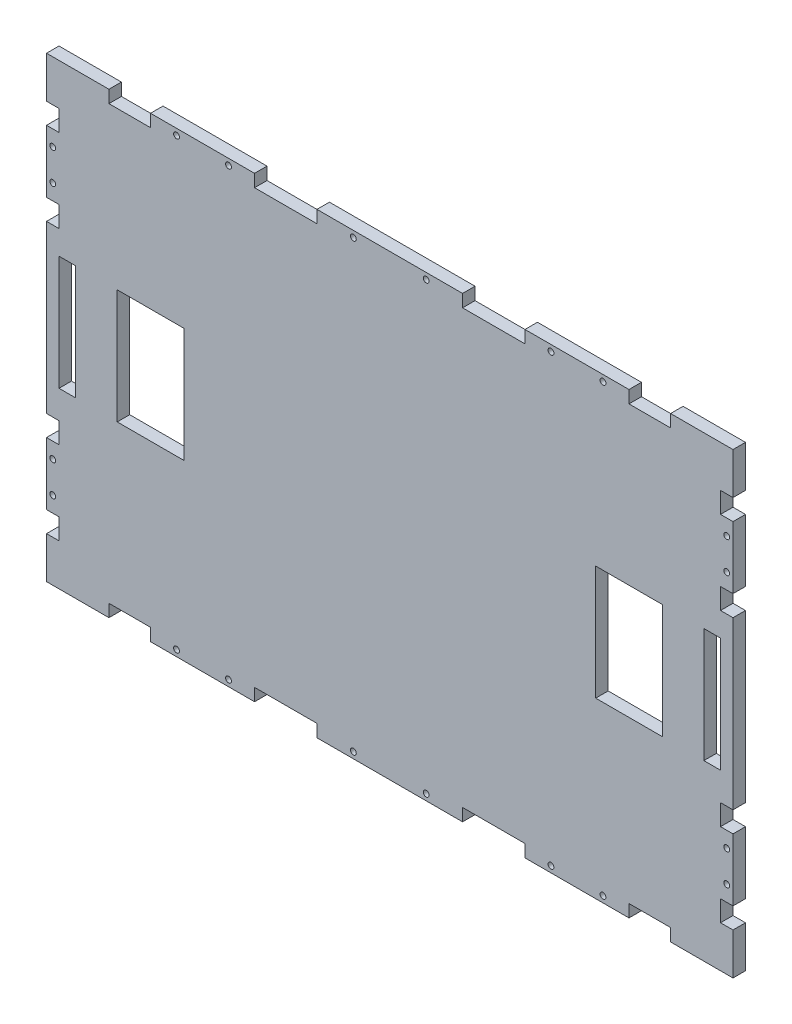
SolidWorks part; units mm, degrees
ref_plane "Plan de face" through (0, 0, 0) normal (0, 0, 1) x (1, 0, 0)
ref_plane "Plan de dessus" through (0, 0, 0) normal (0, 1, 0) x (1, 0, 0)
ref_plane "Plan de droite" through (0, 0, 0) normal (1, 0, 0) x (0, 0, -1)
sketch "Esquisse1" plane through (0, 0, 0) normal (0, 0, 1) x (1, 0, 0)
  line L0 (0, 124.9429) -> (0, -204.46) construction
  line L1 (-165, 110) -> (165, 110)
  line L2 (-165, 110) -> (-165, -110)
  line L3 (-165, -110) -> (165, -110)
  line L4 (165, 110) -> (165, -110)
  line L5 (-211.9802, 0) -> (248.5953, 0) construction
  dimension "D1" = 220
  dimension "D2" = 330
  dimension "D3" = 165
  dimension "D4" = 110
extrude "Boss.-Extru.1" add sketch "Esquisse1" along normal blind 6
sketch "Esquisse2" plane through (0, 0, 6) normal (0, 0, 1) x (1, 0, 0)
  line L0 (-165, 110) -> (-165, -110) construction
  line L1 (-159, 28.5) -> (-151, 28.5)
  line L2 (-159, 28.5) -> (-159, -26.5)
  line L3 (-159, -26.5) -> (-151, -26.5)
  line L4 (-151, 28.5) -> (-151, -26.5)
  line L5 (-131, 28.5) -> (-99, 28.5)
  line L6 (-131, 28.5) -> (-131, -26.5)
  line L7 (-131, -26.5) -> (-99, -26.5)
  line L8 (-99, 28.5) -> (-99, -26.5)
  line L9 (0, 145.0258) -> (0, -189.2208) construction
  line L10 (99, 28.5) -> (99, -26.5)
  line L11 (131, -26.5) -> (99, -26.5)
  line L12 (131, 28.5) -> (131, -26.5)
  line L13 (131, 28.5) -> (99, 28.5)
  line L14 (151, 28.5) -> (151, -26.5)
  line L15 (159, -26.5) -> (151, -26.5)
  line L16 (159, 28.5) -> (159, -26.5)
  line L17 (159, 28.5) -> (151, 28.5)
  line L18 (-165, -110) -> (165, -110) construction
  dimension "D1" = 6
  dimension "D2" = 8
  dimension "D3" = 20
  dimension "D4" = 32
  dimension "D5" = 99
  dimension "D6" = 55
  dimension "D7" = 55
  dimension "D8" = 83.5
  dimension "D9" = 83.5
extrude "Enlèv. mat.-Extru.1" cut sketch "Esquisse2" against normal blind 6
sketch "Esquisse3" plane through (0, 0, 6) normal (0, 0, 1) x (1, 0, 0)
  line L0 (0, 140.8551) -> (0, -222.4606) construction
  line L1 (330.3485, 0) -> (-244.4866, 0) construction
  line L2 (165, 110) -> (-165, 110) construction
  line L3 (-135, 110) -> (-115, 110)
  line L4 (-135, 110) -> (-135, 104)
  line L5 (-135, 104) -> (-115, 104)
  line L6 (-115, 110) -> (-115, 104)
  line L7 (-165, 110) -> (-165, -110) construction
  line L8 (-65, 110) -> (-35, 110)
  line L9 (-65, 110) -> (-65, 104)
  line L10 (-65, 104) -> (-35, 104)
  line L11 (-35, 110) -> (-35, 104)
  line L12 (-165, 50) -> (-159, 50)
  line L13 (-165, 50) -> (-165, 40)
  line L14 (-165, 40) -> (-159, 40)
  line L15 (-159, 50) -> (-159, 40)
  line L16 (35, 110) -> (35, 104)
  line L17 (-165, 90) -> (-159, 90)
  line L18 (-165, 90) -> (-165, 80)
  line L19 (-165, 80) -> (-159, 80)
  line L20 (-159, 90) -> (-159, 80)
  line L21 (65, 104) -> (35, 104)
  line L22 (65, 110) -> (35, 110)
  line L23 (159, 90) -> (159, 80)
  line L24 (165, 80) -> (159, 80)
  line L25 (165, 90) -> (165, 80)
  line L26 (165, 90) -> (159, 90)
  line L27 (159, 50) -> (159, 40)
  line L28 (165, 40) -> (159, 40)
  line L29 (165, 50) -> (165, 40)
  line L30 (165, 50) -> (159, 50)
  line L31 (65, 110) -> (65, 104)
  line L32 (115, 110) -> (115, 104)
  line L33 (135, 104) -> (115, 104)
  line L34 (135, 110) -> (135, 104)
  line L35 (135, 110) -> (115, 110)
  line L36 (135, -110) -> (115, -110)
  line L37 (135, -110) -> (135, -104)
  line L38 (135, -104) -> (115, -104)
  line L39 (115, -110) -> (115, -104)
  line L40 (65, -110) -> (65, -104)
  line L41 (165, -50) -> (159, -50)
  line L42 (165, -50) -> (165, -40)
  line L43 (165, -40) -> (159, -40)
  line L44 (159, -50) -> (159, -40)
  line L45 (165, -90) -> (159, -90)
  line L46 (165, -90) -> (165, -80)
  line L47 (165, -80) -> (159, -80)
  line L48 (159, -90) -> (159, -80)
  line L49 (65, -110) -> (35, -110)
  line L50 (65, -104) -> (35, -104)
  line L51 (-159, -90) -> (-159, -80)
  line L52 (-165, -80) -> (-159, -80)
  line L53 (-165, -90) -> (-165, -80)
  line L54 (-165, -90) -> (-159, -90)
  line L55 (35, -110) -> (35, -104)
  line L56 (-159, -50) -> (-159, -40)
  line L57 (-165, -40) -> (-159, -40)
  line L58 (-165, -50) -> (-165, -40)
  line L59 (-165, -50) -> (-159, -50)
  line L60 (-35, -110) -> (-35, -104)
  line L61 (-65, -104) -> (-35, -104)
  line L62 (-65, -110) -> (-65, -104)
  line L63 (-65, -110) -> (-35, -110)
  line L64 (-115, -110) -> (-115, -104)
  line L65 (-135, -104) -> (-115, -104)
  line L66 (-135, -110) -> (-135, -104)
  line L67 (-135, -110) -> (-115, -110)
  dimension "D1" = 20
  dimension "D2" = 30
  dimension "D3" = 6
  dimension "D4" = 6
  dimension "D5" = 6
  dimension "D6" = 10
  dimension "D7" = 6
  dimension "D8" = 10
  dimension "D9" = 30
  dimension "D10" = 50
  dimension "D11" = 20
  dimension "D12" = 30
extrude "Enlèv. mat.-Extru.2" cut sketch "Esquisse3" against normal blind 6
sketch "Esquisse4" plane through (0, 0, 6) normal (0, 0, 1) x (1, 0, 0)
  line L0 (0, 191.3584) -> (0, -190.3505) construction
  line L1 (361.8037, 0) -> (-270.0648, 0) construction
  line L2 (-165, 80) -> (-165, 50) construction
  line L3 (-115, 104) -> (-115, 110) construction
  line L4 (-65, 110) -> (-115, 110) construction
  line L5 (35, 110) -> (-35, 110) construction
  line L6 (-35, 104) -> (-35, 110) construction
  line L7 (-65, 110) -> (-65, 104) construction
  line L8 (-165, 80) -> (-159, 80) construction
  line L9 (-159, 50) -> (-165, 50) construction
  circle A0 centre (-102.5, 107) radius 1.4
  circle A1 centre (-77.5, 107) radius 1.4
  circle A2 centre (-17.5, 107) radius 1.4
  circle A3 centre (-162, 72.5) radius 1.4
  circle A4 centre (-162, 57.5) radius 1.4
  circle A5 centre (162, 57.5) radius 1.4
  circle A6 centre (162, 72.5) radius 1.4
  circle A7 centre (17.5, 107) radius 1.4
  circle A8 centre (77.5, 107) radius 1.4
  circle A9 centre (102.5, 107) radius 1.4
  circle A10 centre (102.5, -107) radius 1.4
  circle A11 centre (77.5, -107) radius 1.4
  circle A12 centre (17.5, -107) radius 1.4
  circle A13 centre (162, -72.5) radius 1.4
  circle A14 centre (162, -57.5) radius 1.4
  circle A15 centre (-162, -57.5) radius 1.4
  circle A16 centre (-162, -72.5) radius 1.4
  circle A17 centre (-17.5, -107) radius 1.4
  circle A18 centre (-77.5, -107) radius 1.4
  circle A19 centre (-102.5, -107) radius 1.4
  point P29 (-162, 50)
  dimension "D1" = 2.8
  dimension "D2" = 2.8
  dimension "D3" = 2.8
  dimension "D4" = 2.8
  dimension "D5" = 2.8
  dimension "D6" = 3
  dimension "D7" = 3
  dimension "D8" = 12.5
  dimension "D9" = 3
  dimension "D10" = 3
  dimension "D11" = 3
  dimension "D12" = 17.5
  dimension "D13" = 12.5
  dimension "D14" = 7.5
  dimension "D15" = 7.5
extrude "Enlèv. mat.-Extru.3" cut sketch "Esquisse4" against normal blind 6
equation "\"D3@Esquisse1\"=\"D2@Esquisse1\"/2"
equation "\"D4@Esquisse1\"=\"D1@Esquisse1\"/2"
